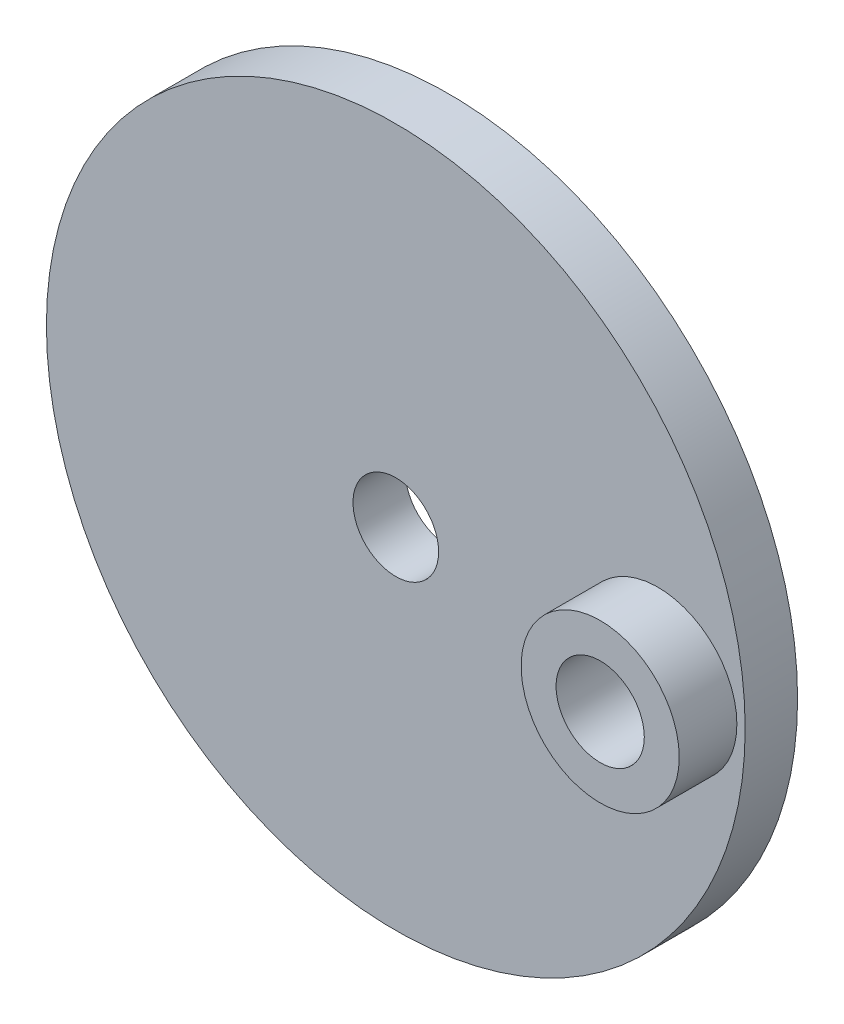
SolidWorks part; units mm, degrees
ref_plane "Front Plane" through (0, 0, 0) normal (0, 0, 1) x (1, 0, 0)
ref_plane "Top Plane" through (0, 0, 0) normal (0, 1, 0) x (1, 0, 0)
ref_plane "Right Plane" through (0, 0, 0) normal (1, 0, 0) x (0, 0, -1)
sketch "Sketch1" plane through (0, 0, 0) normal (0, 0, 1) x (1, 0, 0)
  circle A0 centre (0, 0) radius 20
  dimension "D1" = 40
extrude "Boss-Extrude1" add sketch "Sketch1" along normal blind 3
sketch "Sketch2" plane through (0, 0, 0) normal (0, 0, 1) x (1, 0, 0)
  circle A0 centre (15, 0) radius 2.525
  dimension "D1" = 5.05
  dimension "D2" = 15
extrude "Cut-Extrude3" cut sketch "Sketch2" against normal through all and the other way through all from surface at 3 starting at face at (20, 0, 3)
sketch "Sketch3" plane through (0, 0, 0) normal (0, 0, 1) x (1, 0, 0)
  circle A0 centre (15, 0) radius 2.525
  circle A1 centre (15, 0) radius 4.525
  dimension "D1" = 2
  dimension "D2" = 5.05
extrude "Boss-Extrude2" add sketch "Sketch3" along normal blind 3.3 from surface at 3 starting at face at (17.525, 0, 3)
sketch "Sketch4" plane through (0, 0, 0) normal (0, 0, 1) x (1, 0, 0)
  circle A0 centre (0, 0) radius 2.45
  dimension "D1" = 4.9
extrude "Cut-Extrude4" cut sketch "Sketch4" along normal through all
